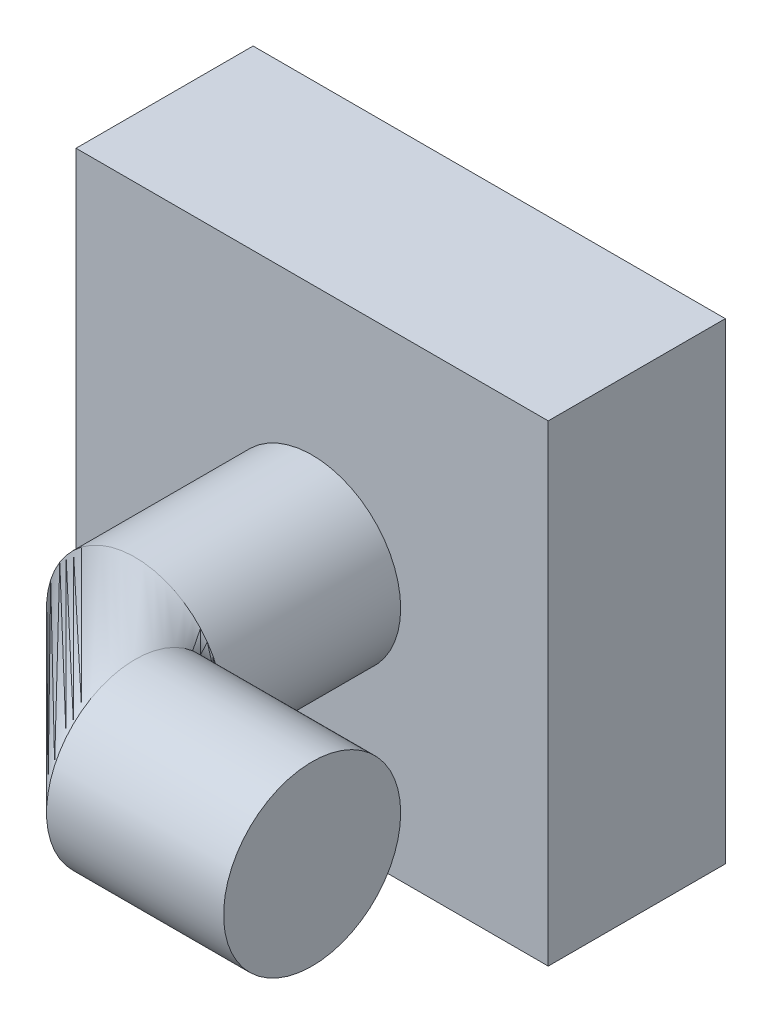
SolidWorks part; units mm, degrees
ref_plane "Front Plane" through (0, 0, 0) normal (0, 0, 1) x (1, 0, 0)
ref_plane "Top Plane" through (0, 0, 0) normal (0, 1, 0) x (1, 0, 0)
ref_plane "Right Plane" through (0, 0, 0) normal (1, 0, 0) x (0, 0, -1)
sketch "Sketch1" plane through (0, 0, 0) normal (0, 1, 0) x (1, 0, 0)
  line L0 (57.15, 0) -> (19.05, 0)
  line L1 (0, 19.05) -> (0, 57.15)
  arc A0 (19.05, 0) -> (0, 19.05) centre (19.05, 19.05) cw
  point P5 (0, 6.35)
  point P7 (18.8746, 0)
  point P8 (0, 0)
  point P9 (0, 19.05)
  point P10 (19.05, 0)
  dimension "D1" = 19.05
  dimension "D2" = 38.1
  dimension "D3" = 38.1
  dimension "D4" = 19.05
ref_plane "Plane1" through (57.15, 0, 0) normal (1, 0, 0) x (0, 0, -1)
sketch "Sketch2" plane through (57.15, 0, 0) normal (1, 0, 0) x (0, 0, -1)
  circle A0 centre (0, 0) radius 19.05
  dimension "D1" = 38.1
sweep "Sweep1" add profiles "Sketch2" path "Sketch1"
sketch "Sketch3" plane through (0, 0, -57.15) normal (0, 0, -1) x (-1, 0, 0)
  line L1 (50.8, 50.8) -> (-50.8, 50.8)
  line L2 (50.8, 50.8) -> (50.8, -50.8)
  line L3 (50.8, -50.8) -> (-50.8, -50.8)
  line L4 (-50.8, 50.8) -> (-50.8, -50.8)
  line L5 (50.8, 50.8) -> (-50.8, -50.8) construction
  line L6 (50.8, -50.8) -> (-50.8, 50.8) construction
  point P0 (0, 0)
  dimension "D1" = 101.6
  dimension "D2" = 101.6
extrude "Boss-Extrude1" add sketch "Sketch3" along normal blind 38.1
